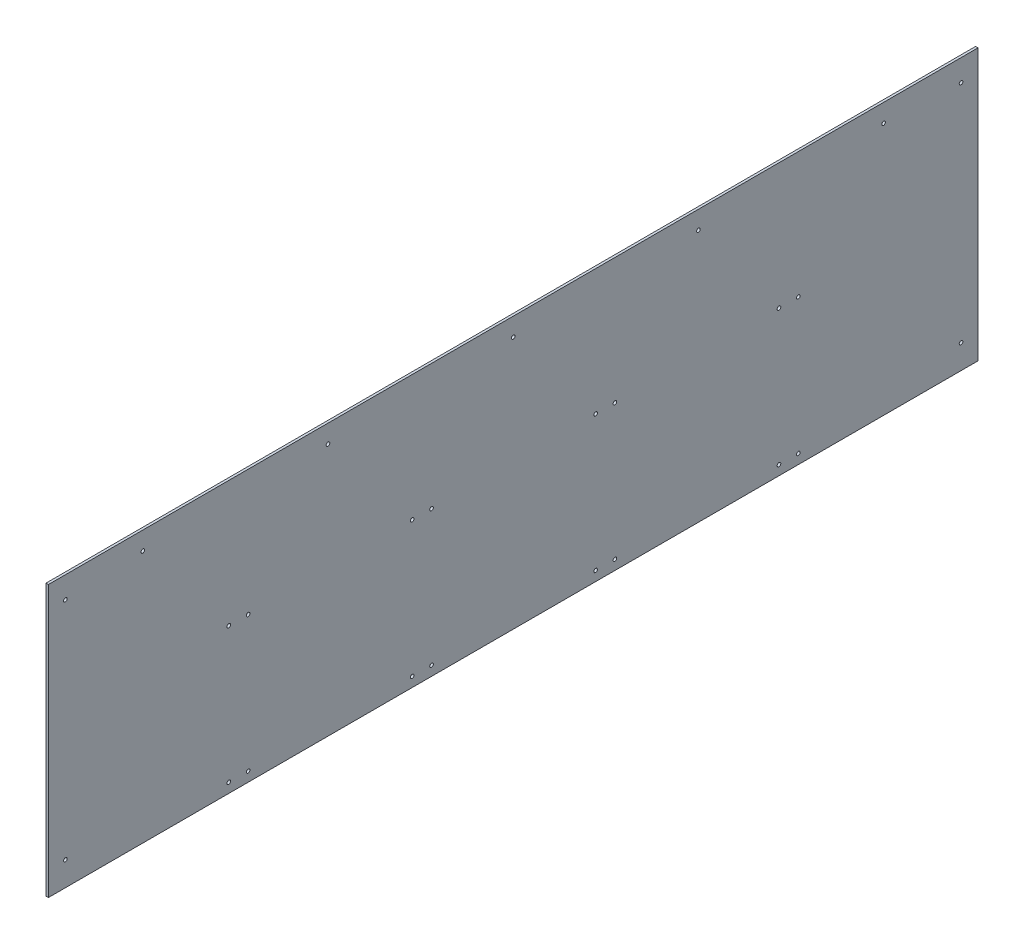
SolidWorks part; units mm, degrees
material "PC High Viscosity"
ref_plane "Front Plane" through (0, 0, 0) normal (0, 0, 1) x (1, 0, 0)
ref_plane "Top Plane" through (0, 0, 0) normal (0, 1, 0) x (1, 0, 0)
ref_plane "Right Plane" through (0, 0, 0) normal (1, 0, 0) x (0, 0, -1)
sketch "Sketch1" plane through (0, 0, 0) normal (1, 0, 0) x (0, 0, -1)
  line L1 (-1219.2, -355.6) -> (1219.2, -355.6)
  line L2 (-1219.2, -355.6) -> (-1219.2, 355.6)
  line L3 (-1219.2, 355.6) -> (1219.2, 355.6)
  line L4 (1219.2, -355.6) -> (1219.2, 355.6)
  line L5 (-1219.2, -355.6) -> (1219.2, 355.6) construction
  line L6 (-1219.2, 355.6) -> (1219.2, -355.6) construction
  point P0 (0, 0)
  dimension "D1" = 711.2
  dimension "D2" = 2438.4
extrude "Boss-Extrude1" add sketch "Sketch1" along normal blind 6.35
hole_wizard "3/8 (0.375) Diameter Hole3" positions "Sketch2" profile "Sketch3" hole size "3/8" standard "ANSI Inch" end condition through all
sketch "Sketch2" plane through (6.35, 0, 0) normal (1, 0, 0) x (0, 0, -1)
  line L0 (-1219.2, -355.6) -> (1219.2, -355.6) construction
  point P0 (-746.125, 25.4)
  point P2 (-695.325, 25.4)
  point P4 (-746.125, -330.2)
  point P6 (-695.325, -330.2)
  dimension "D1" = 50.8
  dimension "D2" = 746.125
  dimension "D3" = 25.4
  dimension "D4" = 381
sketch "Sketch3" plane through (6.35, 25.4, 746.125) normal (0, 1, 0) x (0, 0, -1)
  line L0 (0, 0) -> (0, 6.35)
  line L1 (0, 6.35) -> (4.7625, 6.35)
  line L2 (4.7625, 6.35) -> (4.7625, 0)
  line L5 (4.7625, 0) -> (0, 0)
  line L11 (0, -6.35) -> (0, 107.95) construction
  dimension "Thru Hole Dia." = 9.525
  dimension "Thru Hole Depth" = 6.35
pattern_linear "LPattern1" count 4 spacing 481.076 along (0, 0, -1) of "3/8 (0.375) Diameter Hole3"
hole_wizard "3/8 (0.375) Diameter Hole2" positions "Sketch4" profile "Sketch5" hole size "3/8" standard "ANSI Inch" end condition through all
sketch "Sketch4" plane through (6.35, 0, 0) normal (1, 0, 0) x (0, 0, -1)
  line L0 (1219.2, 355.6) -> (-1219.2, 355.6) construction
  point P0 (-971.55, 307.975)
  dimension "D1" = 971.55
  dimension "D2" = 47.625
sketch "Sketch5" plane through (6.35, 307.975, 971.55) normal (0, 1, 0) x (0, 0, -1)
  line L0 (0, 0) -> (0, 6.35)
  line L1 (0, 6.35) -> (4.7625, 6.35)
  line L2 (4.7625, 6.35) -> (4.7625, 0)
  line L5 (4.7625, 0) -> (0, 0)
  line L11 (0, -6.35) -> (0, 107.95) construction
  dimension "Thru Hole Dia." = 9.525
  dimension "Thru Hole Depth" = 6.35
pattern_linear "LPattern2" count 5 spacing 485.775 along (0, 0, -1) of "3/8 (0.375) Diameter Hole2"
hole_wizard "3/8 (0.375) Diameter Hole1" positions "Sketch6" profile "Sketch7" hole size "3/8" standard "ANSI Inch" end condition through all
sketch "Sketch6" plane through (6.35, 0, 0) normal (1, 0, 0) x (0, 0, -1)
  line L1 (-1219.2, -355.6) -> (1219.2, -355.6) construction
  line L2 (-1219.2, 355.6) -> (-1219.2, -355.6) construction
  line L3 (1219.2, 355.6) -> (-1219.2, 355.6) construction
  point P0 (-1174.75, -292.1)
  point P2 (-1174.75, 298.45)
  dimension "D1" = 57.15
  dimension "D2" = 63.5
  dimension "D3" = 44.45
sketch "Sketch7" plane through (6.35, -292.1, 1174.75) normal (0, 1, 0) x (0, 0, -1)
  line L0 (0, 0) -> (0, 6.35)
  line L1 (0, 6.35) -> (4.7625, 6.35)
  line L2 (4.7625, 6.35) -> (4.7625, 0)
  line L5 (4.7625, 0) -> (0, 0)
  line L11 (0, -6.35) -> (0, 107.95) construction
  dimension "Thru Hole Dia." = 9.525
  dimension "Thru Hole Depth" = 6.35
mirror "Mirror1" about plane through (0, 0, 0) normal (0, 0, 1) of "3/8 (0.375) Diameter Hole1"
